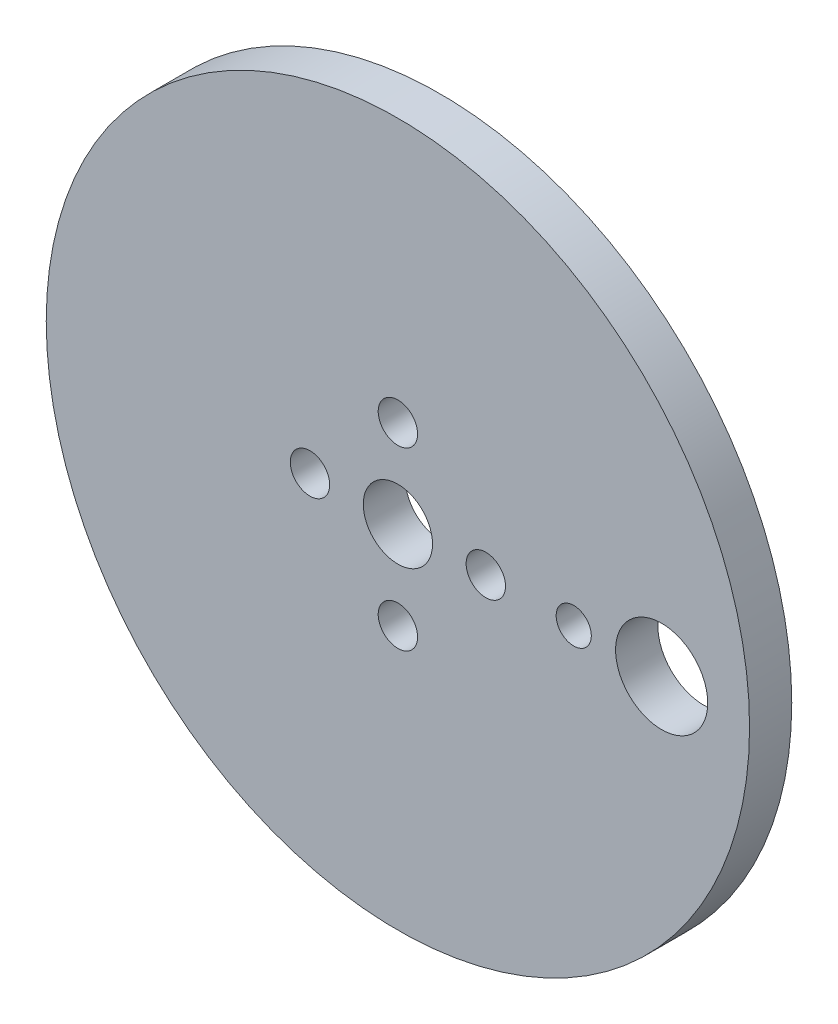
SolidWorks part; units mm, degrees
ref_plane "Front Plane" through (0, 0, 0) normal (0, 0, 1) x (1, 0, 0)
ref_plane "Top Plane" through (0, 0, 0) normal (0, 1, 0) x (1, 0, 0)
ref_plane "Right Plane" through (0, 0, 0) normal (1, 0, 0) x (0, 0, -1)
sketch "Sketch1" plane through (0, 0, 0) normal (0, 0, 1) x (1, 0, 0)
  line L0 (0, 6.35) -> (0, 0) construction
  line L1 (25.4, 0) -> (12.7, 0) construction
  line L2 (19.05, 3.3274) -> (19.05, -5.0123) construction
  line L3 (0, 0) -> (6.35, 0) construction
  circle A0 centre (0, 0) radius 9.525 construction
  circle A1 centre (0, 6.35) radius 1.4224
  circle A2 centre (6.35, 0) radius 1.4224
  circle A3 centre (0, -6.35) radius 1.4224
  circle A4 centre (-6.35, 0) radius 1.4224
  circle A5 centre (0, 0) radius 2.5
  circle A6 centre (0, 0) radius 25.4
  circle A7 centre (19.05, 0) radius 3.3274
  circle A8 centre (12.7, 0) radius 1.27
  point P11 (0, 0)
  point P16 (0, 0)
  dimension "D1" = 2.8448
  dimension "D2" = 19.05
  dimension "D4" = 5
  dimension "D6" = 6.6548
  dimension "D7" = 2.54
  dimension "D10" = 50.8
  dimension "D3" = 6.35
  dimension "D8" = 6.35
  dimension "D9" = 19.05
  dimension "D5" = 4
extrude "Boss-Extrude1" add sketch "Sketch1" along normal blind 3.048
